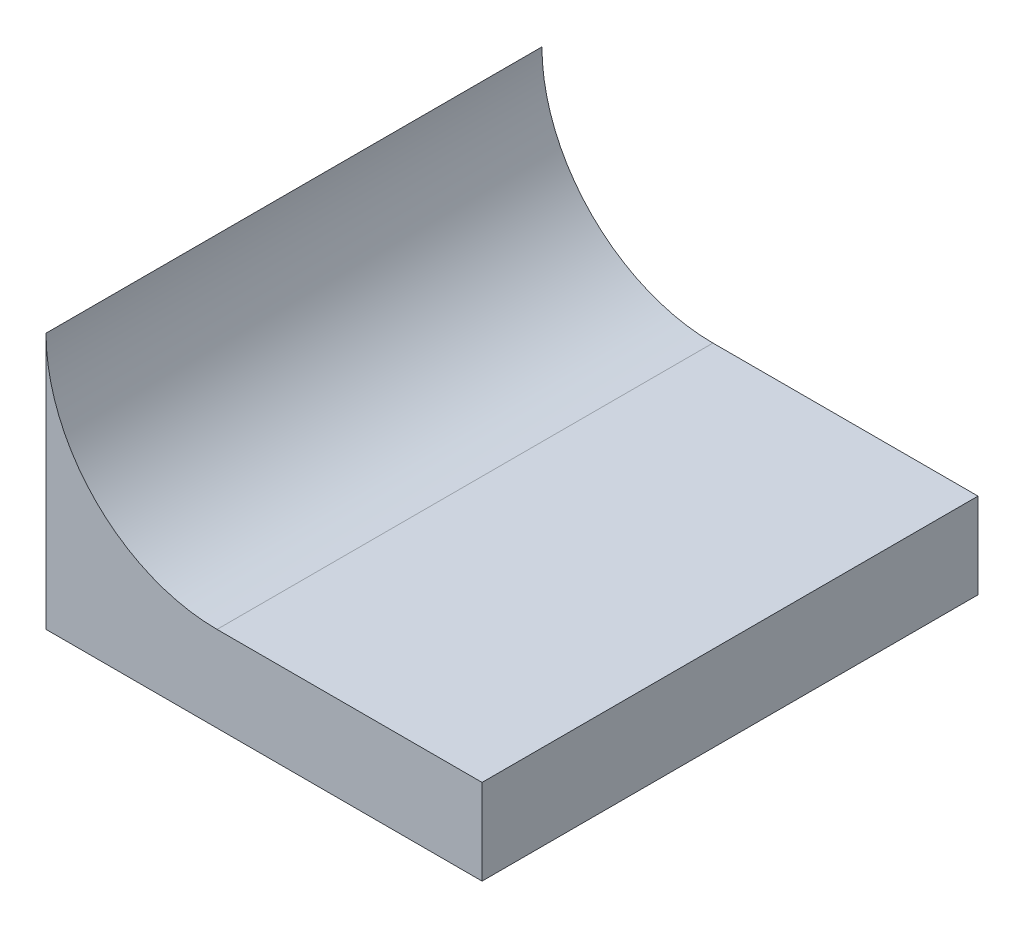
SolidWorks part; units mm, degrees
ref_plane "Front Plane" through (0, 0, 0) normal (0, 0, 1) x (1, 0, 0)
ref_plane "Top Plane" through (0, 0, 0) normal (0, 1, 0) x (1, 0, 0)
ref_plane "Right Plane" through (0, 0, 0) normal (1, 0, 0) x (0, 0, -1)
sketch "Sketch1" plane through (0, 0, 0) normal (0, 0, 1) x (1, 0, 0)
  line L0 (0, 0) -> (0.51, 0)
  line L1 (0.51, 0) -> (0.51, 0.1)
  line L2 (0.51, 0.1) -> (0.2, 0.1)
  line L3 (0, 0.1) -> (0, 0.3) construction
  line L5 (0, 0.3) -> (0.2, 0.3) construction
  line L6 (0, 0.3) -> (0, 0)
  arc A0 (0, 0.3) -> (0.2, 0.1) centre (0.2, 0.3) ccw
  dimension "D1" = 0.2
  dimension "D2" = 0.2
  dimension "D3" = 0.51
  dimension "D4" = 0.1
extrude "Boss-Extrude1" add sketch "Sketch1" along normal mid plane 0.58
